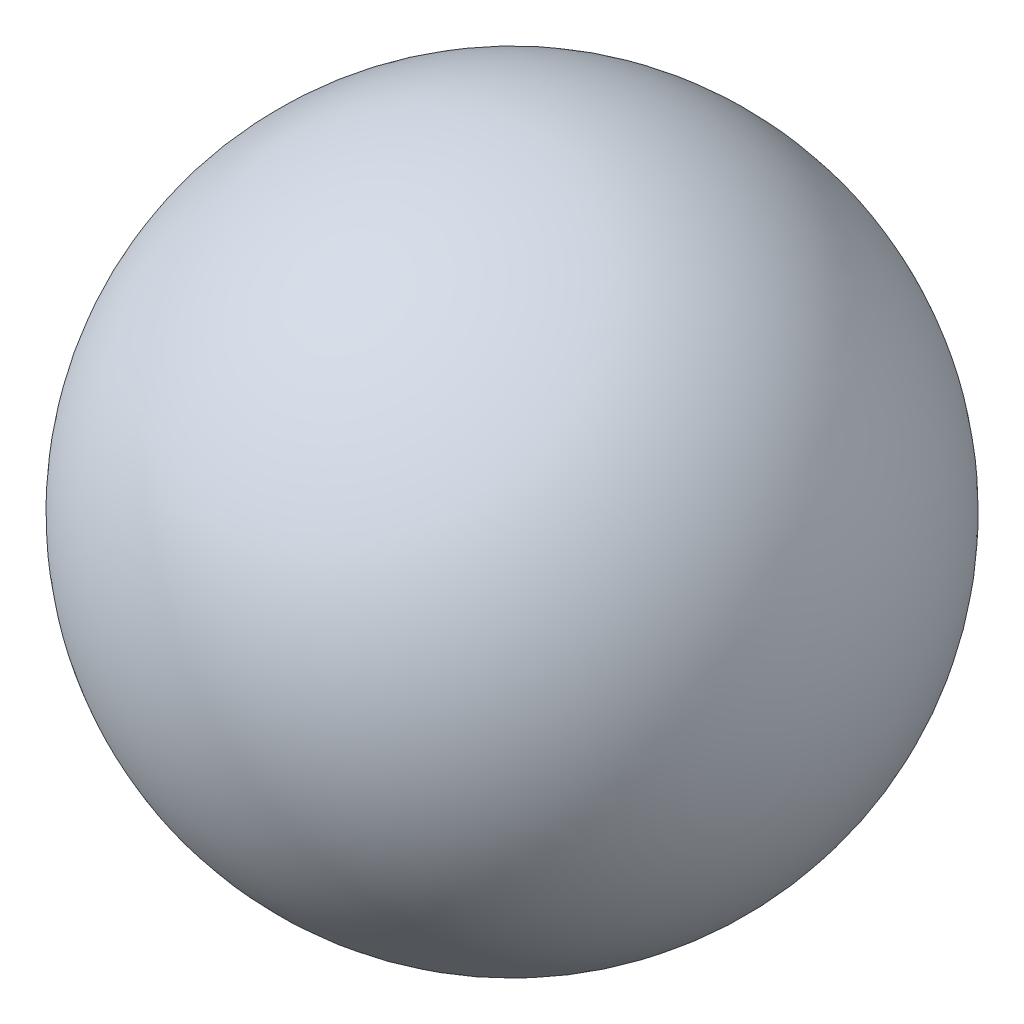
SolidWorks part; units mm, degrees
ref_plane "Front Plane" through (0, 0, 0) normal (0, 0, 1) x (1, 0, 0)
ref_plane "Top Plane" through (0, 0, 0) normal (0, 1, 0) x (1, 0, 0)
ref_plane "Right Plane" through (0, 0, 0) normal (1, 0, 0) x (0, 0, -1)
sketch "Sketch1" plane through (0, 0, 0) normal (0, 1, 0) x (1, 0, 0)
  line L0 (0, 0) -> (0, 609.6)
  arc A0 (0, 609.6) -> (0, 0) centre (0, 304.8) cw
revolve "Revolve1" add sketch "Sketch1" angle 360 about L0
